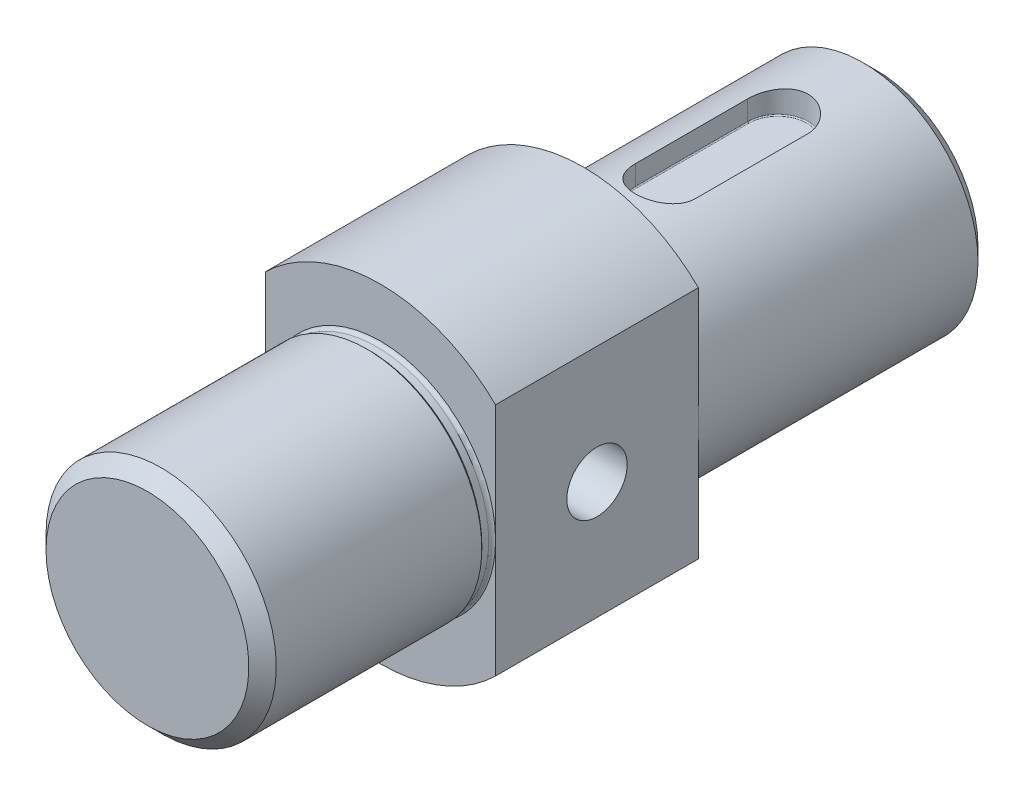
SolidWorks part; units mm, degrees
ref_plane "Спереди" through (0, 0, 0) normal (0, 0, 1) x (1, 0, 0)
ref_plane "Сверху" through (0, 0, 0) normal (0, 1, 0) x (1, 0, 0)
ref_plane "Справа" through (0, 0, 0) normal (1, 0, 0) x (0, 0, -1)
sketch "Эскиз1" plane through (0, 0, 0) normal (1, 0, 0) x (0, 0, -1)
  line L0 (-10676.9003, -2906.2872) -> (-10376.9003, -2906.2872) construction
  line L1 (23.5, 73.5) -> (117.5, 73.5) construction
  line L2 (86.1667, 1.1004) -> (-323.1284, 1.1004) construction
  line L3 (55.9828, 30.0376) -> (118.9828, 30.0376) construction
  line L4 (0, 0) -> (-50000, 0) construction
  line L5 (-122, 0) -> (-122, 42)
  line L6 (-122, 42) -> (-37, 42)
  line L7 (-37, 42) -> (-37, 60)
  line L8 (-37, 60) -> (37, 60)
  line L9 (37, 60) -> (37, 42)
  line L10 (37, 42) -> (144, 42)
  line L11 (144, 42) -> (144, 0)
  line L12 (144, 0) -> (-122, 0)
  line L13 (56.2726, 42) -> (119.2535, 42)
  point P21 (0, 0)
  dimension "D1" = 300
  dimension "D2" = 63
  dimension "D3" = 42
  dimension "D4" = 60
  dimension "D5" = 107
  dimension "D6" = 74
  dimension "D7" = 85
  dimension "D8" = 122
revolve "Повернуть1" add sketch "Эскиз1" angle 360 about L4
ref_plane "Плоскость1" through (0, 42, 0) normal (0, 1, 0) x (1, 0, 0)
sketch "Эскиз2" plane through (0, 42, 0) normal (0, 1, 0) x (1, 0, 0)
  line L0 (0, 67) -> (0, 108) construction
  line L1 (0, -50) -> (0, 50) construction
  line L2 (-11, 67) -> (-11, 108)
  line L3 (11, 67) -> (11, 108)
  line L4 (0, 144) -> (0, 50144) construction
  line L5 (42, 144) -> (-42, 144) construction
  line L6 (60, 37) -> (-60, 37) construction
  arc A0 (-11, 67) -> (11, 67) centre (0, 67) ccw
  arc A1 (11, 108) -> (-11, 108) centre (0, 108) ccw
  point P4 (0, 87.5)
  point P13 (0, 144)
  point P14 (0, 113.4603)
  point P15 (0, 66.1889)
  point P16 (11, 87.5)
  point P17 (0, 119)
  point P18 (0, 56)
  dimension "D1" = 22
  dimension "D2" = 63
  dimension "D3" = 19
extrude "Вырез-Вытянуть1" cut sketch "Эскиз2" against normal blind 9
fillet "Скругление1" radius 0.4 4 edges at (0, 33, -119) (11, 33, -87.5) (0, 33, -56) (-11, 33, -87.5)
chamfer "Фаска1" distance 5 angle 45 1 edges at (-42, 0, -144)
chamfer "Фаска2" distance 5 angle 45 1 edges at (-42, 0, 122)
sketch "Эскиз3" plane through (0, 0, 0) normal (1, 0, 0) x (0, 0, -1)
  line L5 (-37, 42) -> (-42, 42)
  line L7 (-122, 42) -> (-37, 42) construction
  line L8 (-42, 42) -> (-41, 41)
  line L9 (-41, 41) -> (-38.4832, 41)
  line L10 (-38.4832, 41) -> (-42, 41) construction
  line L11 (-42, 42) -> (-42, -49958) construction
  line L12 (-38.4832, 42.6) -> (-42, 42.6) construction
  arc A1 (-37, 42) -> (-38.4832, 41) centre (-38.4832, 42.6) cw
  point P4 (-39.5, 42)
  point P6 (-38.6002, 41)
  dimension "D3" = 1
  dimension "D4" = 1.6
  dimension "D1" = 45
  dimension "D2" = 5
revolve "Вырез-Повернуть1" cut sketch "Эскиз3" angle 360 about L4
ref_plane "Плоскость2" through (0, 60, 0) normal (0, 1, 0) x (1, 0, 0)
sketch "Эскиз5" plane through (0, 60, 0) normal (0, 1, 0) x (1, 0, 0)
  line L0 (0, 139) -> (0, 50139) construction
  line L1 (42, 139) -> (-42, 139) construction
  line L2 (42, 55.4999) -> (42, 50055.4999) construction
  line L4 (-42, -37) -> (-60, -37)
  line L5 (42, 37) -> (60, 37)
  line L6 (42, 37) -> (42, -37)
  line L7 (42, -37) -> (60, -37)
  line L8 (60, 37) -> (60, -37)
  line L9 (-60, 37) -> (-60, -37)
  line L10 (-42, 37) -> (-60, 37)
  line L11 (-42, 37) -> (-42, -37)
  point P4 (0, 139)
  point P11 (0, 0)
  point P12 (60, 37)
  point P15 (42, 37)
extrude "Вырез-Вытянуть2" cut sketch "Эскиз5" against normal blind 120
sketch "Эскиз6" plane through (42, 0, 0) normal (1, 0, 0) x (0, 0, -1)
  circle A0 centre (0, 0) radius 11
  dimension "D1" = 22
extrude "Вырез-Вытянуть3" cut sketch "Эскиз6" against normal blind 54.05
ref_plane "Плоскость3" through (0, 0, 0) normal (0, 0, 1) x (1, 0, 0)
sketch "Эскиз7" plane through (0, 0, 0) normal (0, 0, 1) x (1, 0, 0)
  line L0 (-49.0464, -0.6497) -> (44.9536, -0.6497) construction
  line L1 (-21, 0) -> (49979, 0) construction
  line L2 (-12.05, -11) -> (-12.05, 11) construction
  line L3 (-12.05, -11) -> (-12.05, 11) construction
  line L5 (-12.05, 11) -> (-12.05, 0)
  line L10 (-12.05, 0) -> (-21.2801, 0)
  line L11 (-21.2801, 0) -> (-12.05, 11)
  dimension "D1" = 50
revolve "Вырез-Повернуть6" cut sketch "Эскиз7" angle 360 about L1
